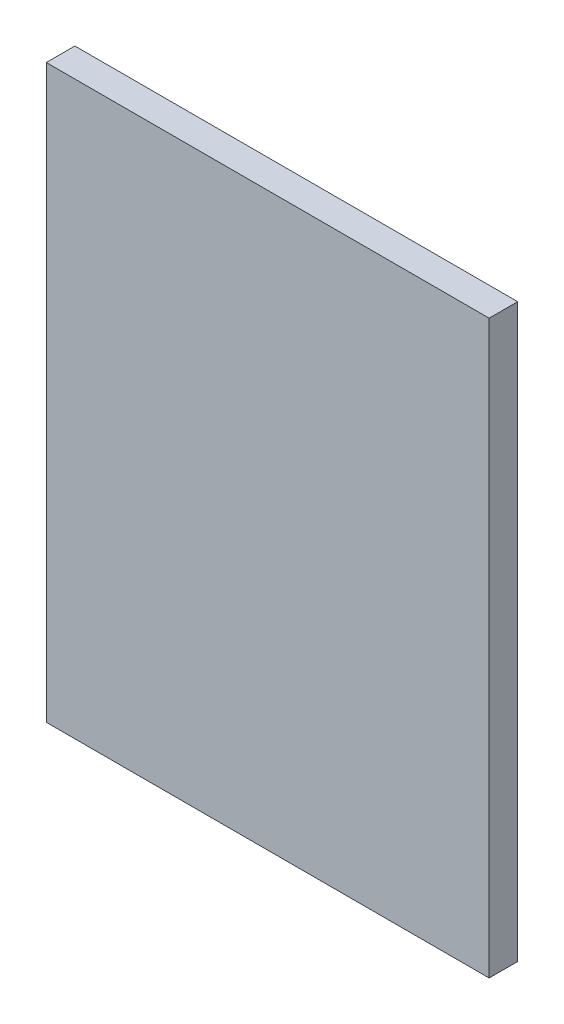
SolidWorks part; units mm, degrees
material "Plain Carbon Steel"
ref_plane "Front Plane" through (0, 0, 0) normal (0, 0, 1) x (1, 0, 0)
ref_plane "Top Plane" through (0, 0, 0) normal (0, 1, 0) x (1, 0, 0)
ref_plane "Right Plane" through (0, 0, 0) normal (1, 0, 0) x (0, 0, -1)
sketch "Sketch1" plane through (0, 0, 0) normal (0, 0, 1) x (1, 0, 0)
  line L1 (0, 0) -> (155, 0)
  line L2 (0, 0) -> (0, 200)
  line L3 (0, 200) -> (155, 200)
  line L4 (155, 0) -> (155, 200)
  dimension "D1" = 200
  dimension "D2" = 155
extrude "Bottom Outer Casing" add sketch "Sketch1" along normal blind 10
